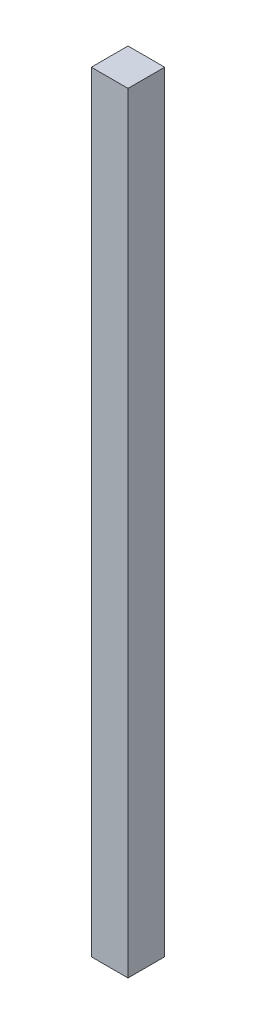
SolidWorks part; units mm, degrees
ref_plane "Front Plane" through (0, 0, 0) normal (0, 0, 1) x (1, 0, 0)
ref_plane "Top Plane" through (0, 0, 0) normal (0, 1, 0) x (1, 0, 0)
ref_plane "Right Plane" through (0, 0, 0) normal (1, 0, 0) x (0, 0, -1)
sketch "Sketch1" plane through (0, 0, 0) normal (0, 1, 0) x (1, 0, 0)
  line L1 (0, 0) -> (20, 0)
  line L2 (0, 0) -> (0, -20)
  line L3 (0, -20) -> (20, -20)
  line L4 (20, 0) -> (20, -20)
extrude "Boss-Extrude1" add sketch "Sketch1" along normal blind 420
